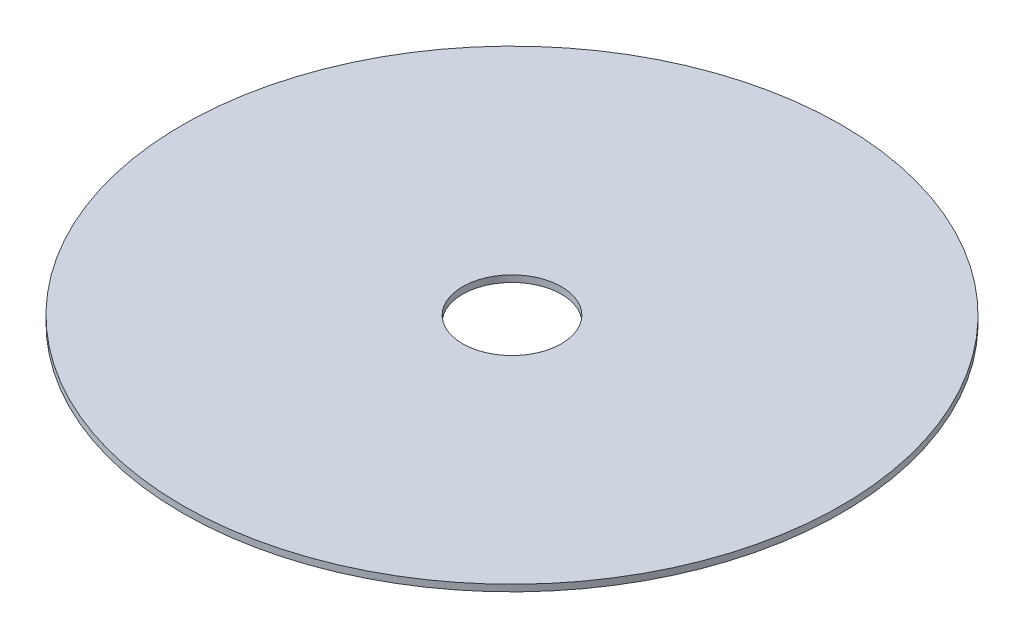
SolidWorks part; units mm, degrees
ref_plane "Front" through (0, 0, 0) normal (0, 0, 1) x (1, 0, 0)
ref_plane "Top" through (0, 0, 0) normal (0, 1, 0) x (1, 0, 0)
ref_plane "Right" through (0, 0, 0) normal (1, 0, 0) x (0, 0, -1)
sketch "Sketch1" plane through (0, 0, 0) normal (0, 1, 0) x (1, 0, 0)
  circle A0 centre (0, 0) radius 9
  circle A1 centre (0, 0) radius 60
  dimension "D1" = 18
  dimension "D2" = 120
extrude "Boss-Extrude1" add sketch "Sketch1" along normal blind 1.2
